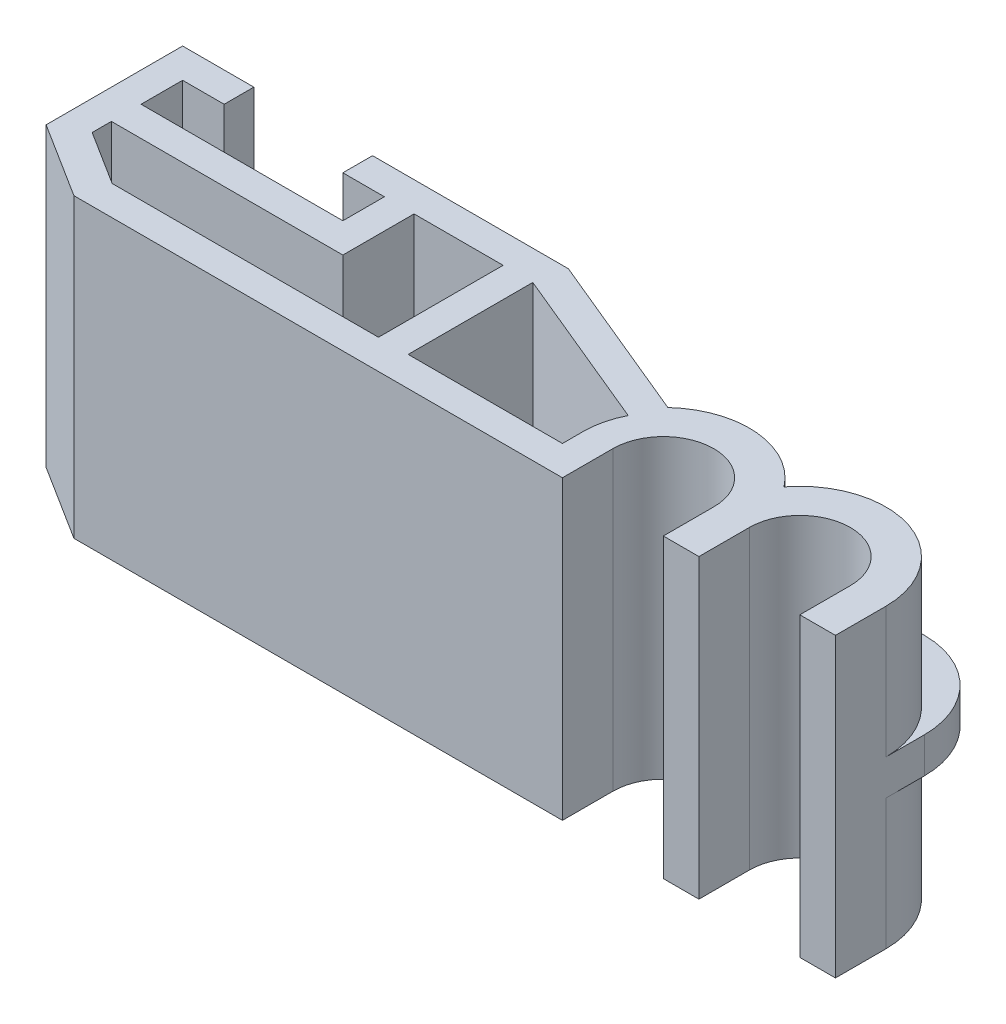
SolidWorks part; units mm, degrees
ref_plane "Front Plane" through (0, 0, 0) normal (0, 0, 1) x (1, 0, 0)
ref_plane "Top Plane" through (0, 0, 0) normal (0, 1, 0) x (1, 0, 0)
ref_plane "Right Plane" through (0, 0, 0) normal (1, 0, 0) x (0, 0, -1)
sketch "Sketch1" plane through (0, 0, 0) normal (0, 1, 0) x (1, 0, 0)
  line L0 (0, 0) -> (50000, 0) construction
  line L1 (-1.7, 0) -> (-1.7, -1.7)
  line L2 (1.7, -1.7) -> (-1.7, -1.7) construction
  line L3 (1.7, -1.7) -> (1.7, 1.7) construction
  line L4 (1.7, 1.7) -> (-1.7, 1.7) construction
  line L5 (-1.7, -1.7) -> (-1.7, 1.7) construction
  line L6 (1.7, -1.7) -> (-1.7, 1.7) construction
  line L7 (1.7, 1.7) -> (-1.7, -1.7) construction
  line L8 (-1.7, -1.7) -> (-2.9, -1.7)
  line L9 (1.7, -1.7) -> (2.9, -1.7)
  line L10 (-2.9, -1.7) -> (-2.9, 0)
  line L11 (2.9, -1.7) -> (2.9, 0)
  line L12 (2.3, -1.7) -> (2.3, 49998.3) construction
  line L13 (1.7, 0) -> (1.7, -1.7)
  line L14 (6.3, 0) -> (6.3, -1.7)
  line L15 (6.3, -1.7) -> (7.5, -1.7)
  line L16 (7.5, -1.7) -> (7.5, 0)
  line L17 (1.7, -1.7) -> (1.7, 0)
  line L18 (2.9, 0) -> (2.9, -1.7)
  arc A1 (-1.7, 0) -> (1.7, 0) centre (0, 0) cw
  arc A3 (2.9, 0) -> (6.3, 0) centre (4.6, 0) cw
  arc A4 (7.5, 0) -> (2.3, 1.7664) centre (4.6, 0) ccw
  arc A5 (-2.9, 0) -> (2.3, 1.7664) centre (0, 0) cw
  point P17 (2.3, -1.7)
  dimension "D1" = 1.7
  dimension "D2" = 1.2
  dimension "D3" = 1.2
extrude "Boss-Extrude1" add sketch "Sketch1" along normal blind 10 contours A5 L10 L8 L1 A1 L13 L9 L11 A3 L14 L15 L16 A4
sketch "Sketch2" plane through (0, 0, 0) normal (0, -1, 0) x (1, 0, 0)
  line L0 (-2.9, 1.7) -> (-20.7, 1.7)
  line L1 (-20.7, 1.7) -> (-20.7, -4.5)
  line L2 (-20.7, -4.5) -> (-7.7, -4.5)
  line L3 (-7.7, -4.5) -> (-1.9726, -2.1257)
  line L4 (-2.9, 1.7) -> (-2.9, 0) construction
  line L5 (-2.9, 0) -> (-2.9, 1.7)
  arc A0 (-2.9, 0) -> (2.3, -1.7664) centre (0, 0) ccw construction
  arc A1 (-1.9726, -2.1257) -> (-2.9, 0) centre (0, 0) cw
  dimension "D1" = 17.8
  dimension "D2" = 6.2
  dimension "D3" = 13
  dimension "D4" = 6.2
extrude "Boss-Extrude2" add sketch "Sketch2" against normal up to surface (10 mm away) up to face at (2.3, 10, 0.1006)
sketch "Sketch3" plane through (0, 0, 0) normal (0, -1, 0) x (1, 0, 0)
  line L0 (-20.7, -4.5) -> (-20.7, 0.1) construction
  line L1 (-20.7, 1.7) -> (-20.7, -4.5) construction
  line L2 (-1.7, 1.7) -> (-18.1623, 1.7) construction
  line L3 (-1.7, 1.7) -> (-20.7, 1.7) construction
  line L4 (-18.1623, 1.7) -> (-20.7, 0.1)
  line L5 (-20.7, 0.1) -> (-20.7, 1.7)
  line L6 (-20.7, 1.7) -> (-18.1623, 1.7)
  dimension "D1" = 3
  dimension "D2" = 4.6
extrude "Cut-Extrude1" cut sketch "Sketch3" against normal up to surface (10 mm away) up to face at (-0.9774, 10, -0.5932)
shell "Shell2" thickness 1
sketch "Sketch4" plane through (0, 1, 0) normal (0, 1, 0) x (1, 0, 0)
  line L0 (-2.7, -0.7) -> (-17.8734, -0.7) construction
  line L1 (-7.8991, 3.5) -> (-8.8991, 3.5)
  line L2 (-7.8991, 3.5) -> (-7.8991, -0.7)
  line L3 (-7.8991, -0.7) -> (-8.8991, -0.7)
  line L4 (-8.8991, 3.5) -> (-8.8991, -0.7)
  line L5 (-7.8991, 3.5) -> (-8.8991, -0.7) construction
  line L6 (-7.8991, -0.7) -> (-8.8991, 3.5) construction
  point P4 (-8.3991, 1.4)
  dimension "D1" = 1
extrude "Boss-Extrude3" add sketch "Sketch4" along normal up to surface (9 mm away) up to face at (-10.4359, 10, -1.0418)
sketch "Sketch7" plane through (0, 1, 0) normal (0, 1, 0) x (1, 0, 0)
  line L0 (-19.7, 3.5) -> (-8.8991, 3.5) construction
  line L1 (-12.9, 3.5) -> (-11.9, 3.5)
  line L2 (-12.9, 3.5) -> (-12.9, 1.1)
  line L3 (-12.9, 1.1) -> (-11.9, 1.1)
  line L4 (-11.9, 3.5) -> (-11.9, 1.1)
  line L5 (-12.9, 3.5) -> (-11.9, 1.1) construction
  line L6 (-12.9, 1.1) -> (-11.9, 3.5) construction
  line L7 (-20.7, -0.1) -> (-20.7, 4.5) construction
  line L11 (-20.7, 4.5) -> (-7.7, 4.5) construction
  line L13 (-19.7, 0.4517) -> (-19.7, 3.5) construction
  line L14 (-12.9, 1.1) -> (-19.7, 1.1)
  line L15 (-12.9, 1.1) -> (-12.9, 2.1)
  line L16 (-12.9, 2.1) -> (-19.7, 2.1)
  line L17 (-19.7, 1.1) -> (-19.7, 2.1)
  line L18 (-12.9, 1.1) -> (-19.7, 2.1) construction
  line L19 (-12.9, 2.1) -> (-19.7, 1.1) construction
  point P4 (-12.4, 2.3)
  point P14 (-16.3, 1.6)
  line M7 (-8.8991, 3.5) -> (-19.7, 3.5)
  line M8 (-19.7, 3.5) -> (-19.7, 0.4517)
  dimension "D1" = 1
  dimension "D2" = 8.8
  dimension "D3" = 3.4
  dimension "D4" = 1
extrude "Boss-Extrude4" add sketch "Sketch7" along normal up to surface (9 mm away) contours L2 L16 L14 M8 | L4 L2 L3 M7 up to face at (-4.7355, 10, -0.6681)
sketch "Sketch8" plane through (0, 10, 0) normal (0, 1, 0) x (1, 0, 0)
  line L0 (-19.7, 3.5) -> (-12.9, 3.5) construction
  line L1 (-20.7, 4.5) -> (-18.3, 4.5) construction
  line L2 (-20.7, 4.5) -> (-20.7, 3.5) construction
  line L3 (-20.7, 3.5) -> (-18.3, 3.5) construction
  line L4 (-18.3, 4.5) -> (-18.3, 3.5) construction
  line L5 (-20.7, 4.5) -> (-18.3, 3.5) construction
  line L6 (-20.7, 3.5) -> (-18.3, 4.5) construction
  line L7 (-20.7, 4.5) -> (-7.7, 4.5) construction
  line L8 (-11.9, 3.5) -> (-14.3, 3.5) construction
  line L9 (-11.9, 3.5) -> (-11.9, 4.5) construction
  line L10 (-11.9, 4.5) -> (-14.3, 4.5) construction
  line L11 (-14.3, 3.5) -> (-14.3, 4.5) construction
  line L12 (-11.9, 3.5) -> (-14.3, 4.5) construction
  line L13 (-11.9, 4.5) -> (-14.3, 3.5) construction
  line L15 (-18.3, 4.5) -> (-14.3, 4.5)
  line L16 (-18.3, 4.5) -> (-18.3, 3.5)
  line L17 (-18.3, 3.5) -> (-14.3, 3.5)
  line L18 (-14.3, 4.5) -> (-14.3, 3.5)
  line L19 (-18.3, 4.5) -> (-14.3, 3.5) construction
  line L20 (-18.3, 3.5) -> (-14.3, 4.5) construction
  point P4 (-19.5, 4)
  point P12 (-13.1, 4)
  point P17 (-16.3, 4)
  dimension "D1" = 2.4
extrude "Cut-Extrude2" cut sketch "Sketch8" against normal blind 8.8
ref_plane "Plane1" through (0, 5, 0) normal (0, 1, 0) x (1, 0, 0)
sketch "Sketch9" plane through (0, 5, 0) normal (0, 1, 0) x (1, 0, 0)
  line L0 (0, 2.9) -> (0, 4.2) construction
  line L1 (0, 4.2) -> (-6.9763, 4.2)
  line L2 (-7.7, 4.5) -> (-1.9726, 2.1257) construction
  line L3 (0, 4.2) -> (4.6, 4.2)
  line L4 (4.6, 0) -> (4.6, 50000) construction
  line L5 (7.5, -1.7) -> (7.5, 49998.3) construction
  line L6 (7.5, 0) -> (7.5, 1.2998)
  line L7 (-1.9726, 2.1257) -> (-6.9763, 4.2)
  arc A0 (2.3, 1.7664) -> (-1.9726, 2.1257) centre (0, 0) ccw construction
  arc A1 (4.6, 4.2) -> (7.5, 1.2998) centre (4.6, 1.3) cw
  arc A2 (7.5, 0) -> (2.3, 1.7664) centre (4.6, 0) ccw
  arc A3 (7.5, 0) -> (2.3, 1.7664) centre (4.6, 0) ccw construction
  arc A4 (2.3, 1.7664) -> (-1.9726, 2.1257) centre (0, 0) ccw
  dimension "D1" = 1.3
extrude "Boss-Extrude5" add sketch "Sketch9" along normal mid plane 1.2
